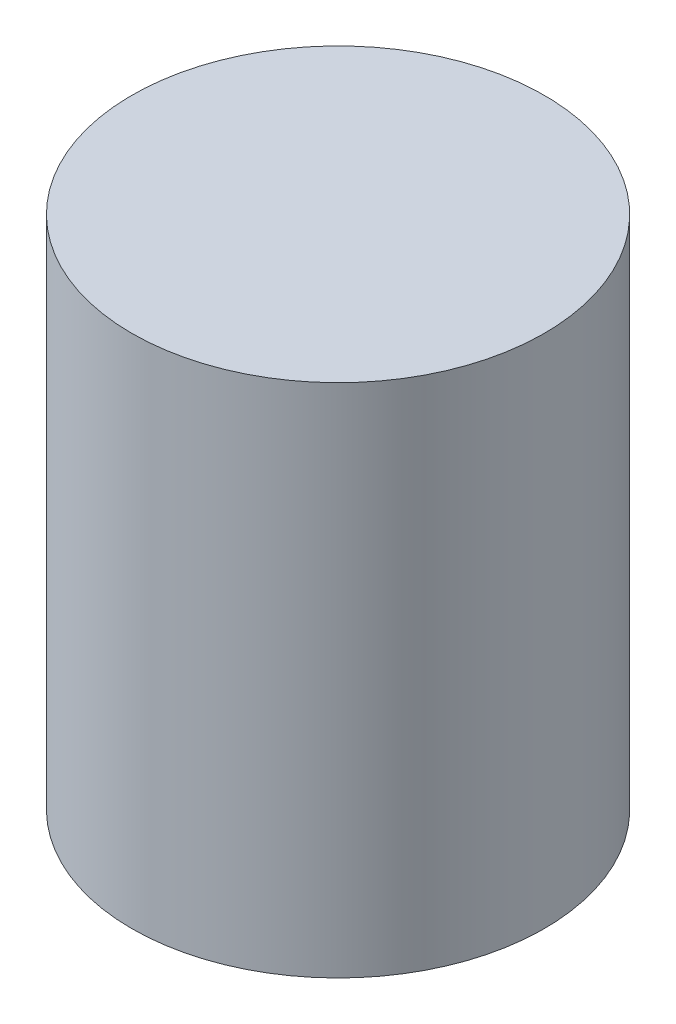
SolidWorks part; units mm, degrees
ref_plane "前视基准面" through (0, 0, 0) normal (0, 0, 1) x (1, 0, 0)
ref_plane "上视基准面" through (0, 0, 0) normal (0, 1, 0) x (1, 0, 0)
ref_plane "右视基准面" through (0, 0, 0) normal (1, 0, 0) x (0, 0, -1)
sketch "草图1" plane through (0, 0, 0) normal (0, 1, 0) x (1, 0, 0)
  circle A0 centre (0, 0) radius 20
extrude "凸台-拉伸1" add sketch "草图1" along normal blind 50
